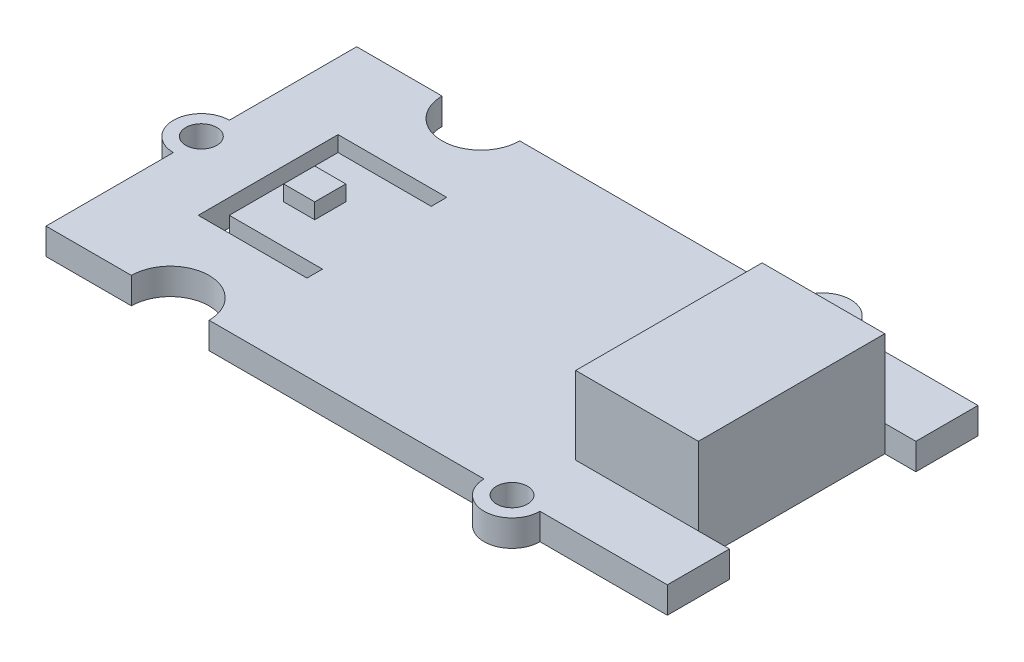
SolidWorks part; units mm, degrees
ref_plane "Front" through (0, 0, 0) normal (0, 0, 1) x (1, 0, 0)
ref_plane "Top" through (0, 0, 0) normal (0, 1, 0) x (1, 0, 0)
ref_plane "Right" through (0, 0, 0) normal (1, 0, 0) x (0, 0, -1)
sketch "Sketch1" plane through (0, 0, 0) normal (0, 1, 0) x (1, 0, 0)
  line L0 (0, 0) -> (0, 8.2)
  line L1 (0, 20) -> (5.5, 20)
  line L2 (40, 20) -> (40, 16)
  line L3 (40, 0) -> (31.8, 0)
  line L4 (4.3, 14.5) -> (11.3, 14.5)
  line L5 (11.3, 14.5) -> (11.3, 13.5)
  line L6 (11.3, 13.5) -> (5.3, 13.5)
  line L7 (5.3, 13.5) -> (5.3, 6.5)
  line L8 (5.3, 6.5) -> (11.3, 6.5)
  line L9 (11.3, 6.5) -> (11.3, 5.5)
  line L10 (11.3, 5.5) -> (4.3, 5.5)
  line L11 (4.3, 5.5) -> (4.3, 14.5)
  line L12 (40, 16) -> (38, 16)
  line L13 (38, 16) -> (38, 4)
  line L14 (38, 4) -> (40, 4)
  line L15 (0, 10) -> (46.7688, 10) construction
  line L16 (0, 11.8) -> (0, 20)
  line L17 (10.5, 20) -> (28.2, 20)
  line L18 (5.5, 0) -> (0, 0)
  line L19 (31.8, 20) -> (40, 20)
  line L20 (40, 4) -> (40, 0)
  line L22 (28.2, 0) -> (10.5, 0)
  arc A0 (0, 11.8) -> (0, 8.2) centre (0, 10) ccw
  circle A1 centre (0, 10) radius 1
  arc A2 (5.5, 20) -> (10.5, 20) centre (8, 20) ccw
  arc A3 (10.5, 0) -> (5.5, 0) centre (8, 0) ccw
  arc A4 (31.8, 20) -> (28.2, 20) centre (30, 20) ccw
  circle A6 centre (30, 0) radius 1
  circle A7 centre (30, 20) radius 1
  arc A9 (28.2, 0) -> (31.8, 0) centre (30, 0) ccw
  dimension "D3" = 2
  dimension "D4" = 0.8
  dimension "D12" = 2.5
  dimension "D14" = 2
  dimension "D1" = 40
  dimension "D2" = 20
  dimension "D5" = 10
  dimension "D6" = 1
  dimension "D7" = 1
  dimension "D8" = 1
  dimension "D9" = 9
  dimension "D10" = 11.3
  dimension "D11" = 0
  dimension "D13" = 8
  dimension "D15" = 12
  dimension "D16" = 30
  dimension "D17" = 7
extrude "Boss-Extrude1" add sketch "Sketch1" along normal blind 1.7
sketch "Sketch2" plane through (0, 1.7, 0) normal (0, 1, 0) x (1, 0, 0)
  line L0 (0, 10) -> (42.2016, 10) construction
  line L1 (6.3, 11) -> (8.3, 11)
  line L2 (6.3, 11) -> (6.3, 9)
  line L3 (6.3, 9) -> (8.3, 9)
  line L4 (8.3, 11) -> (8.3, 9)
  line L5 (5.3, 6.5) -> (5.3, 13.5) construction
  dimension "D1" = 2
  dimension "D2" = 2
  dimension "D3" = 1
extrude "Boss-Extrude2" add sketch "Sketch2" along normal blind 1
sketch "Sketch3" plane through (0, 1.7, 0) normal (0, 1, 0) x (1, 0, 0)
  line L0 (0, 10) -> (44.7815, 10) construction
  line L1 (38, 16) -> (30.1, 16)
  line L2 (38, 16) -> (38, 4)
  line L3 (38, 4) -> (30.1, 4)
  line L4 (30.1, 16) -> (30.1, 4)
  dimension "D1" = 12
  dimension "D2" = 7.9
extrude "Boss-Extrude3" add sketch "Sketch3" along normal blind 5
